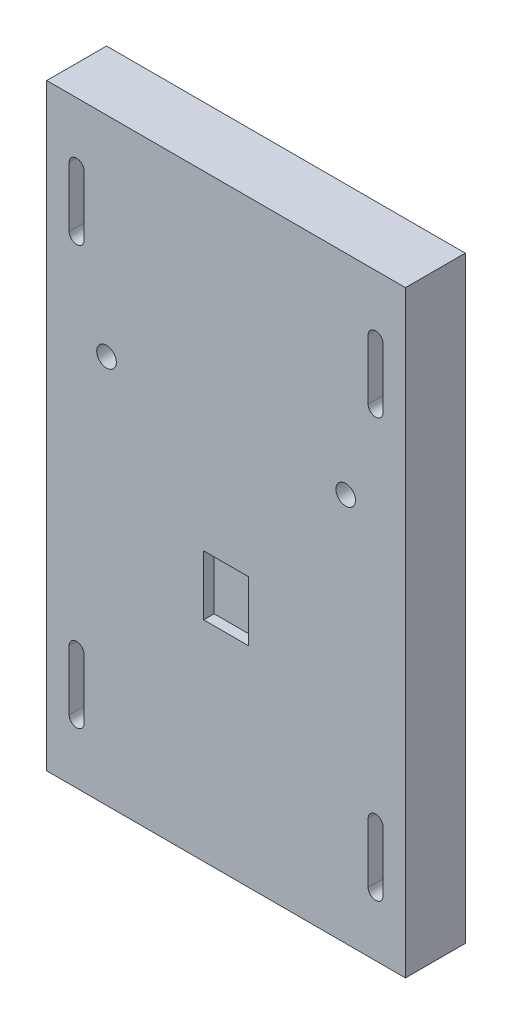
SolidWorks part; units mm, degrees
ref_plane "Front Plane" through (0, 0, 0) normal (0, 0, 1) x (1, 0, 0)
ref_plane "Top Plane" through (0, 0, 0) normal (0, 1, 0) x (1, 0, 0)
ref_plane "Right Plane" through (0, 0, 0) normal (1, 0, 0) x (0, 0, -1)
sketch "Sketch1" plane through (0, 0, 0) normal (0, 0, 1) x (1, 0, 0)
  line L1 (0, 0) -> (76.2, 0)
  line L2 (0, 0) -> (0, 127)
  line L3 (0, 127) -> (76.2, 127)
  line L4 (76.2, 0) -> (76.2, 127)
extrude "Boss-Extrude1" add sketch "Sketch1" along normal blind 12.7
sketch "Sketch2" plane through (0, 0, 12.7) normal (0, 0, 1) x (1, 0, 0)
  line L0 (71.4375, 12.7) -> (71.4375, 25.4)
  line L1 (7.9375, 12.7) -> (7.9375, 25.4)
  line L2 (4.7625, 12.7) -> (4.7625, 25.4)
  line L3 (68.2625, 12.7) -> (68.2625, 25.4)
  line L4 (7.9375, 101.6) -> (7.9375, 114.3)
  line L5 (4.7625, 101.6) -> (4.7625, 114.3)
  line L6 (71.4375, 101.6) -> (71.4375, 114.3)
  line L7 (68.2625, 101.6) -> (68.2625, 114.3)
  arc A0 (7.9375, 12.7) -> (4.7625, 12.7) centre (6.35, 12.7) cw
  arc A1 (7.9375, 25.4) -> (4.7625, 25.4) centre (6.35, 25.4) ccw
  arc A2 (71.4375, 12.7) -> (68.2625, 12.7) centre (69.85, 12.7) cw
  arc A3 (71.4375, 25.4) -> (68.2625, 25.4) centre (69.85, 25.4) ccw
  arc A4 (7.9375, 101.6) -> (4.7625, 101.6) centre (6.35, 101.6) cw
  arc A5 (7.9375, 114.3) -> (4.7625, 114.3) centre (6.35, 114.3) ccw
  arc A6 (71.4375, 101.6) -> (68.2625, 101.6) centre (69.85, 101.6) cw
  arc A7 (71.4375, 114.3) -> (68.2625, 114.3) centre (69.85, 114.3) ccw
  dimension "D1" = 2
  dimension "D2" = 2
extrude "Cut-Extrude1" cut sketch "Sketch2" against normal blind 6.35
sketch "Sketch3" plane through (0, 0, 0) normal (0, 0, -1) x (-1, 0, 0)
  line L0 (-23.6855, 96.8375) -> (-10.9855, 96.8375)
  line L1 (-65.0875, 96.8375) -> (-52.3875, 96.8375)
  line L2 (-65.0875, 100.0125) -> (-52.3875, 100.0125)
  line L3 (-23.6855, 100.0125) -> (-10.9855, 100.0125)
  line L4 (-65.0875, 26.9875) -> (-52.3875, 26.9875)
  line L5 (-65.0875, 30.1625) -> (-52.3875, 30.1625)
  line L6 (-23.6855, 26.9875) -> (-10.9855, 26.9875)
  line L7 (-23.6855, 30.1625) -> (-10.9855, 30.1625)
  arc A0 (-65.0875, 96.8375) -> (-65.0875, 100.0125) centre (-65.0875, 98.425) cw
  arc A1 (-52.3875, 96.8375) -> (-52.3875, 100.0125) centre (-52.3875, 98.425) ccw
  arc A2 (-23.6855, 96.8375) -> (-23.6855, 100.0125) centre (-23.6855, 98.425) cw
  arc A3 (-10.9855, 96.8375) -> (-10.9855, 100.0125) centre (-10.9855, 98.425) ccw
  arc A4 (-65.0875, 26.9875) -> (-65.0875, 30.1625) centre (-65.0875, 28.575) cw
  arc A5 (-52.3875, 26.9875) -> (-52.3875, 30.1625) centre (-52.3875, 28.575) ccw
  arc A6 (-23.6855, 26.9875) -> (-23.6855, 30.1625) centre (-23.6855, 28.575) cw
  arc A7 (-10.9855, 26.9875) -> (-10.9855, 30.1625) centre (-10.9855, 28.575) ccw
  dimension "D1" = 2
  dimension "D2" = 2
extrude "Cut-Extrude2" cut sketch "Sketch3" against normal blind 6.35
sketch "Sketch4" plane through (0, 0, 12.7) normal (0, 0, 1) x (1, 0, 0)
  line L1 (33.3375, 57.15) -> (42.8625, 57.15)
  line L2 (33.3375, 57.15) -> (33.3375, 44.45)
  line L3 (33.3375, 44.45) -> (42.8625, 44.45)
  line L4 (42.8625, 57.15) -> (42.8625, 44.45)
extrude "Cut-Extrude3" cut sketch "Sketch4" against normal blind 2.2225
sketch "Sketch5" plane through (0, 0, 12.7) normal (0, 0, 1) x (1, 0, 0)
  circle A0 centre (12.7, 82.55) radius 2.0828
  circle A1 centre (63.5, 82.55) radius 2.0828
extrude "Cut-Extrude4" cut sketch "Sketch5" against normal blind 25.4
